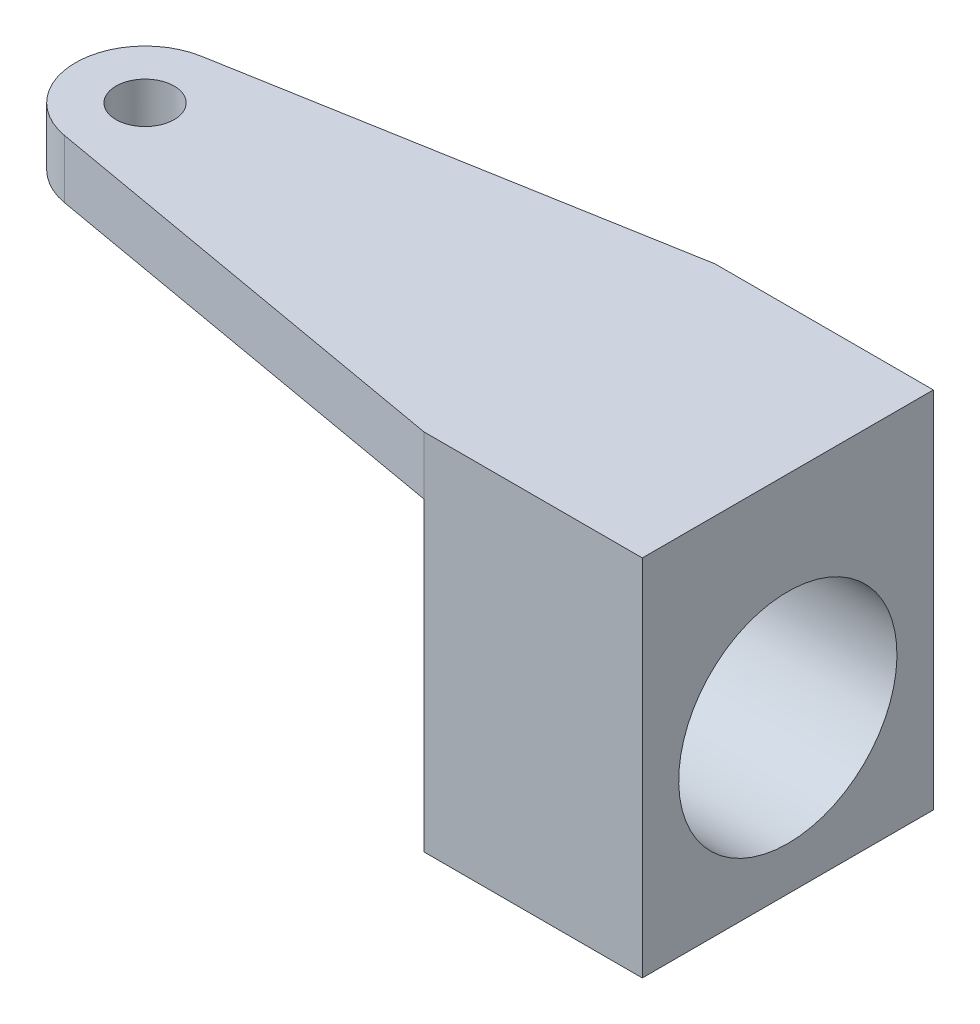
SolidWorks part; units mm, degrees
material "Plain Carbon Steel"
ref_plane "Front Plane" through (0, 0, 0) normal (0, 0, 1) x (1, 0, 0)
ref_plane "Top Plane" through (0, 0, 0) normal (0, 1, 0) x (1, 0, 0)
ref_plane "Right Plane" through (0, 0, 0) normal (1, 0, 0) x (0, 0, -1)
sketch "Sketch1" plane through (0, 0, 0) normal (0, -1, 0) x (-1, 0, 0)
  line L0 (-220.8473, 50) -> (-145.8473, 50)
  line L1 (-145.8473, 50) -> (4.1527, 23.551)
  line L2 (-220.8473, -50) -> (-220.8473, 50)
  line L3 (4.1527, -23.551) -> (-145.8473, -50)
  line L4 (-145.8473, -50) -> (-220.8473, -50)
  line L5 (0, 0) -> (-220.8473, 0) construction
  circle A0 centre (0, 0) radius 10
  arc A1 (4.1527, 23.551) -> (4.1527, -23.551) centre (0, 0) cw
  dimension "D3" = 20
  dimension "D1" = 225
  dimension "D2" = 100
  dimension "D4" = 75
  dimension "D5" = 170
extrude "Boss-Extrude1" add sketch "Sketch1" along normal blind 125
sketch "Sketch2" plane through (0, -125, 0) normal (0, -1, 0) x (-1, 0, 0)
  line L1 (-145.8473, 50) -> (-145.8473, -50)
  line L3 (4.1527, 23.551) -> (-145.8473, 50) construction
  line L5 (-145.8473, -50) -> (4.1527, -23.551) construction
  line L6 (4.1527, 23.551) -> (-145.8473, 50)
  line L7 (-145.8473, -50) -> (4.1527, -23.551)
  arc A1 (4.1527, -23.551) -> (4.1527, 23.551) centre (0, 0) ccw construction
  arc A2 (4.1527, -23.551) -> (4.1527, 23.551) centre (0, 0) ccw
extrude "Cut-Extrude1" cut sketch "Sketch2" against normal offset from surface (105 mm away) 20 up to face at (117.5537, 0, 0)
sketch "Sketch5" plane through (145.8473, 0, 0) normal (-1, 0, 0) x (0, 0, -1)
  line L0 (50, 125) -> (-50, 20) construction
  line L1 (23.551, 20) -> (-23.551, 20) construction
  circle A0 centre (0, 72.5) radius 37.5
  dimension "D1" = 75
extrude "Cut-Extrude2" cut sketch "Sketch5" against normal through all
